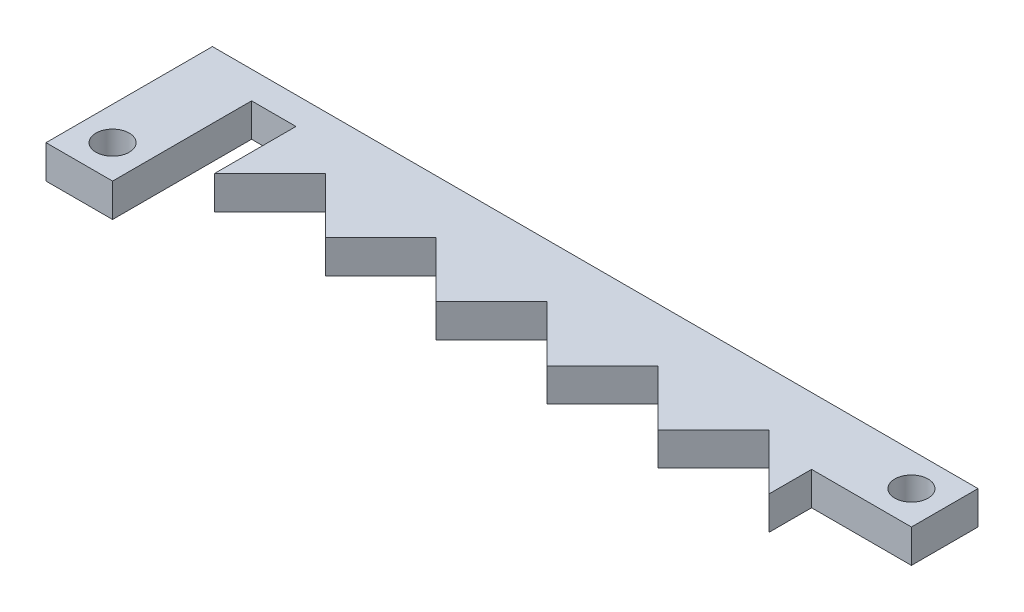
SolidWorks part; units mm, degrees
ref_plane "Front Plane" through (0, 0, 0) normal (0, 0, 1) x (1, 0, 0)
ref_plane "Top Plane" through (0, 0, 0) normal (0, 1, 0) x (1, 0, 0)
ref_plane "Right Plane" through (0, 0, 0) normal (1, 0, 0) x (0, 0, -1)
sketch "Sketch1" plane through (0, 0, 0) normal (0, 1, 0) x (1, 0, 0)
  line L0 (0, 42.3412) -> (0, 38.3412)
  line L1 (0, 38.3412) -> (5, 43.3412)
  line L2 (5, 43.3412) -> (10, 38.3412)
  line L3 (10, 38.3412) -> (15, 43.3412)
  line L4 (15, 43.3412) -> (20, 38.3412)
  line L5 (20, 38.3412) -> (25, 43.3412)
  line L6 (25, 43.3412) -> (30, 38.3412)
  line L7 (30, 38.3412) -> (35, 43.3412)
  line L8 (35, 43.3412) -> (40, 38.3412)
  line L9 (40, 38.3412) -> (45, 43.3412)
  line L10 (45, 43.3412) -> (50, 38.3412)
  line L15 (5, 48.1688) -> (58.9437, 48.1688)
  line L16 (50, 42.1688) -> (50, 38.3412)
  line L20 (0, 42.3412) -> (0, 45.6968)
  line L26 (-1.8488, 48.1688) -> (-10, 48.1688)
  line L27 (5, 48.1688) -> (-1.8488, 48.1688)
  line L28 (-10, 48.1688) -> (-10, 33.1688)
  line L29 (-10, 33.1688) -> (-4, 33.1688)
  line L30 (-4, 33.1688) -> (-4, 45.6968)
  line L31 (-4, 45.6968) -> (0, 45.6968)
  line L32 (-10, 36.1688) -> (-4, 36.1688) construction
  line L33 (58.9437, 48.1688) -> (59, 48.1688)
  line L34 (59, 48.1688) -> (59, 42.1688)
  line L35 (59, 42.1688) -> (50, 42.1688)
  line L36 (56, 48.1688) -> (56, 42.1688) construction
  circle A2 centre (-7, 36.1688) radius 1.5
  circle A3 centre (56, 45.1688) radius 1.5
  point P2 (51.3231, 38.3412)
  point P20 (0, 0)
  point P21 (58.9437, 48.1688)
  dimension "D7" = 3
  dimension "D9" = 6
  dimension "D11" = 3
  dimension "D1" = 10
  dimension "D2" = 5
  dimension "D3" = 6
  dimension "D5" = 15
  dimension "D6" = 10
  dimension "D8" = 3
  dimension "D10" = 9
  dimension "D12" = 3
  dimension "D13" = 50
  dimension "D4" = 5
extrude "Boss-Extrude1" add sketch "Sketch1" along normal blind 3
